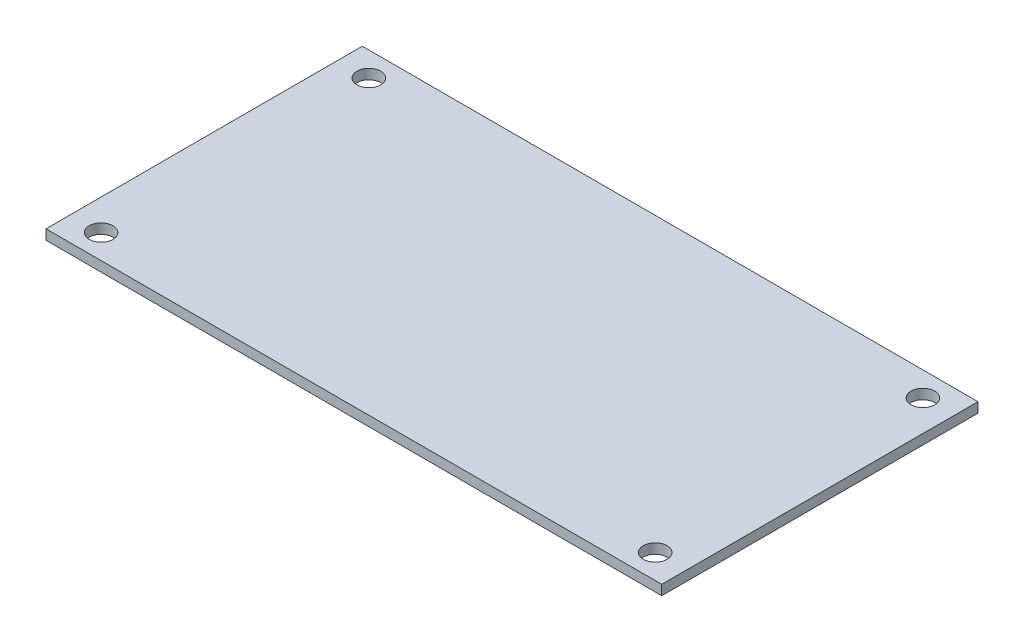
SolidWorks part; units mm, degrees
ref_plane "Front Plane" through (0, 0, 0) normal (0, 0, 1) x (1, 0, 0)
ref_plane "Top Plane" through (0, 0, 0) normal (0, 1, 0) x (1, 0, 0)
ref_plane "Right Plane" through (0, 0, 0) normal (1, 0, 0) x (0, 0, -1)
sketch "Sketch1" plane through (0, 0, 0) normal (0, 1, 0) x (1, 0, 0)
  line L0 (4.95, 46.9) -> (93.95, 3.9) construction
  line L1 (0, 0) -> (98.9, 0)
  line L2 (0, 0) -> (0, 50.8)
  line L3 (0, 50.8) -> (98.9, 50.8)
  line L4 (98.9, 0) -> (98.9, 50.8)
  line L5 (4.95, 46.9) -> (93.95, 46.9) construction
  line L6 (4.95, 46.9) -> (4.95, 3.9) construction
  line L7 (4.95, 3.9) -> (93.95, 3.9) construction
  line L8 (93.95, 46.9) -> (93.95, 3.9) construction
  line L9 (0, 0) -> (98.9, 50.8) construction
  circle A0 centre (4.95, 46.9) radius 1.905
  circle A1 centre (93.95, 46.9) radius 1.905
  circle A2 centre (93.95, 3.9) radius 1.905
  circle A3 centre (4.95, 3.9) radius 1.905
  point P11 (49.45, 25.4)
  dimension "D3" = 3.81
  dimension "D1" = 50.8
  dimension "D2" = 98.9
  dimension "D4" = 89
  dimension "D5" = 43
extrude "Boss-Extrude1" add sketch "Sketch1" along normal blind 1.6
ref_plane "Plane1" through (49.45, 0, 0) normal (-1, 0, 0) x (0, 0, 1)
